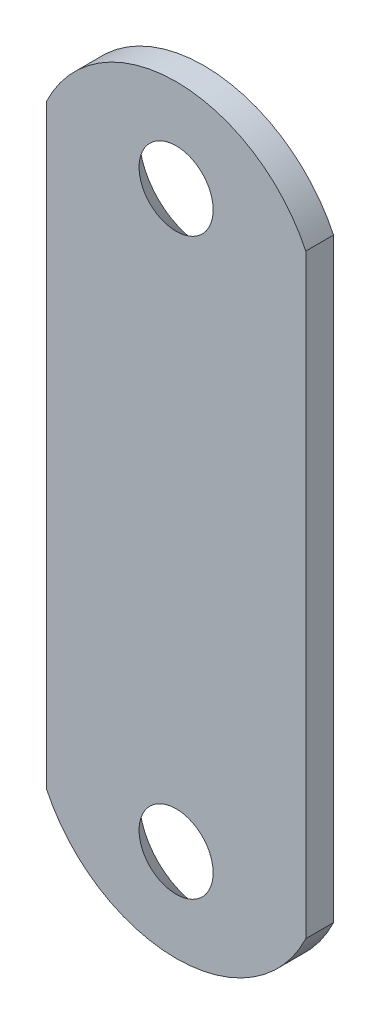
SolidWorks part; units mm, degrees
ref_plane "Front Plane" through (0, 0, 0) normal (0, 0, 1) x (1, 0, 0)
ref_plane "Top Plane" through (0, 0, 0) normal (0, 1, 0) x (1, 0, 0)
ref_plane "Right Plane" through (0, 0, 0) normal (1, 0, 0) x (0, 0, -1)
sketch "Sketch1" plane through (0, 0, 0) normal (0, 0, 1) x (1, 0, 0)
  line L0 (0, 29.8652) -> (0, -27.0072) construction
  line L1 (-17.3834, 0) -> (13.0962, 0) construction
  line L3 (-7, 16.076) -> (-7, -16.076)
  line L5 (7, 16.076) -> (7, -16.076)
  arc A2 (7, 16.076) -> (-7, 16.076) centre (0, 12.75) ccw
  arc A3 (7, -16.076) -> (-7, -16.076) centre (0, -12.75) cw
  dimension "D2" = 41
  dimension "D1" = 14
  dimension "D3" = 25.5
extrude "Extrude1" add sketch "Sketch1" along normal blind 1.5
sketch "Sketch2" plane through (0, 0, 0) normal (1, 0, 0) x (0, 0, -1)
  line L0 (-16.9591, -15.5) -> (23.1172, -15.5) construction
  line L1 (0, -15.5) -> (0, -12)
  line L2 (0, -16.076) -> (0, 16.076) construction
  line L4 (0, -12) -> (-1.5, -13.5)
  line L5 (-1.5, -13.5) -> (-1.5, -15.5)
  line L6 (-1.5, -15.5) -> (0, -15.5)
  line L7 (-11.9811, 0) -> (11.8209, 0) construction
  dimension "D1" = 45
  dimension "D2" = 4
  dimension "D3" = 1.5
  dimension "D4" = 31
revolve "Cut-Revolve2" cut sketch "Sketch2" angle 360 about L0
mirror "Mirror1" about plane through (0, 0, 0) normal (0, 1, 0) of "Cut-Revolve2"
